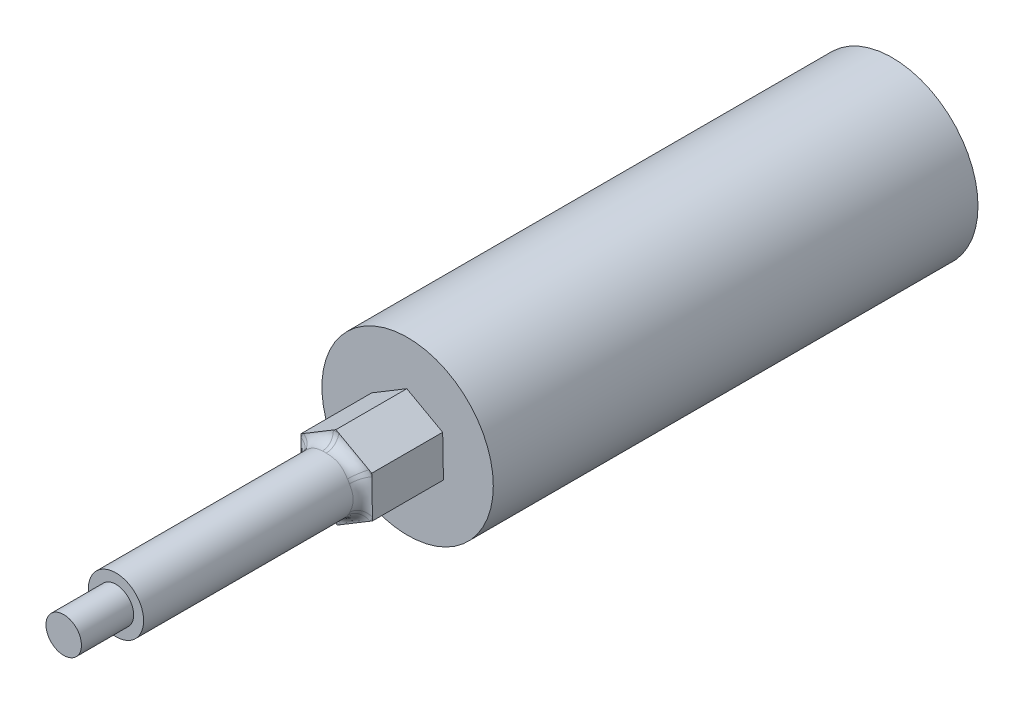
SolidWorks part; units mm, degrees
ref_plane "Front Plane" through (0, 0, 0) normal (0, 0, 1) x (1, 0, 0)
ref_plane "Top Plane" through (0, 0, 0) normal (0, 1, 0) x (1, 0, 0)
ref_plane "Right Plane" through (0, 0, 0) normal (1, 0, 0) x (0, 0, -1)
sketch "Sketch2" plane through (0, 0, 0) normal (0, 0, 1) x (1, 0, 0)
  circle A0 centre (0, 0) radius 7.25
  dimension "D1" = 14.5
extrude "Boss-Extrude1" add sketch "Sketch2" along normal blind 41
sketch "Sketch3" plane through (0, 0, 41) normal (0, 0, 1) x (1, 0, 0)
  line L1 (3.032, -1.6754) -> (2.967, 1.7881)
  line L2 (2.967, 1.7881) -> (-0.065, 3.4635)
  line L3 (-0.065, 3.4635) -> (-3.032, 1.6754)
  line L4 (-3.032, 1.6754) -> (-2.967, -1.7881)
  line L5 (-2.967, -1.7881) -> (0.065, -3.4635)
  line L6 (0.065, -3.4635) -> (3.032, -1.6754)
  circle A1 centre (0, 0) radius 3 construction
  dimension "D1" = 6
extrude "Boss-Extrude2" add sketch "Sketch3" along normal blind 6
sketch "Sketch4" plane through (0, 0, 47) normal (0, 0, 1) x (1, 0, 0)
  circle A0 centre (0, 0) radius 2.34
  dimension "D1" = 4.68
extrude "Boss-Extrude3" add sketch "Sketch4" along normal blind 18.67
fillet "Fillet1" radius 1 1 edges at (2.34, 0, 47)
sketch "Sketch5" plane through (0, 0, 65.67) normal (0, 0, 1) x (1, 0, 0)
  circle A0 centre (0, 0) radius 1.5
  dimension "D1" = 3
extrude "Boss-Extrude4" add sketch "Sketch5" along normal blind 4.42
